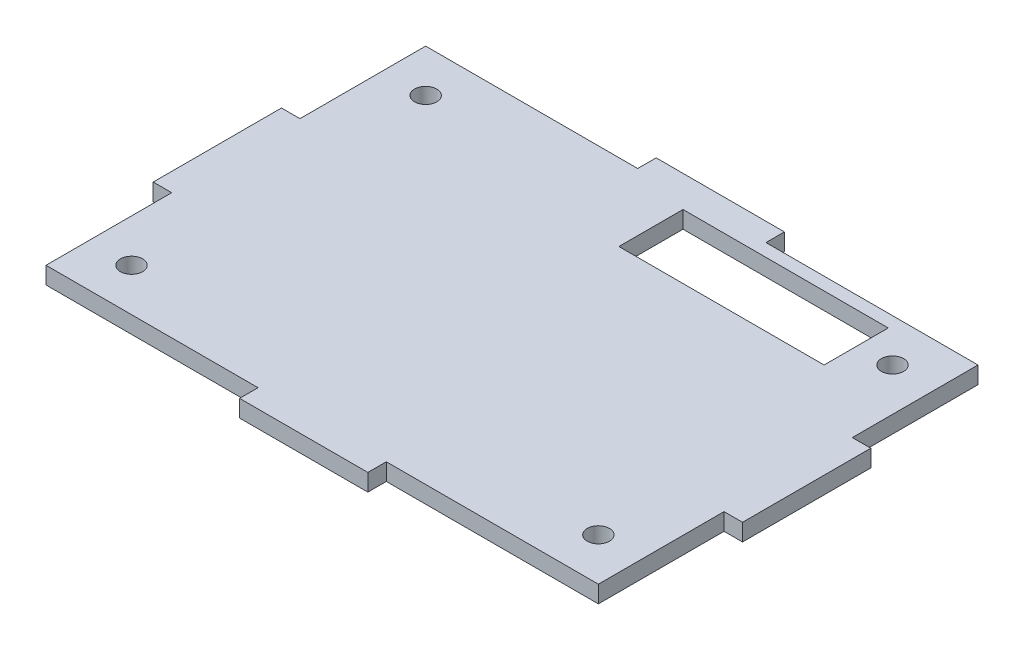
SolidWorks part; units mm, degrees
ref_plane "Front Plane" through (0, 0, 0) normal (0, 0, 1) x (1, 0, 0)
ref_plane "Top Plane" through (0, 0, 0) normal (0, 1, 0) x (1, 0, 0)
ref_plane "Right Plane" through (0, 0, 0) normal (1, 0, 0) x (0, 0, -1)
sketch "Sketch1" plane through (0, 0, 0) normal (0, 1, 0) x (1, 0, 0)
  line L1 (41.021, -28.194) -> (-41.021, -28.194)
  line L2 (41.021, -28.194) -> (41.021, 28.194)
  line L3 (41.021, 28.194) -> (-41.021, 28.194)
  line L4 (-41.021, -28.194) -> (-41.021, 28.194)
  line L5 (41.021, -28.194) -> (-41.021, 28.194) construction
  line L6 (41.021, 28.194) -> (-41.021, -28.194) construction
  line L7 (-34.671, 21.844) -> (34.671, 21.844) construction
  line L8 (-34.671, 21.844) -> (-34.671, -21.844) construction
  line L9 (-34.671, -21.844) -> (34.671, -21.844) construction
  line L10 (34.671, 21.844) -> (34.671, -21.844) construction
  line L11 (-34.671, 21.844) -> (34.671, -21.844) construction
  line L12 (-34.671, -21.844) -> (34.671, 21.844) construction
  circle A0 centre (-34.671, 21.844) radius 1.651
  circle A1 centre (-34.671, -21.844) radius 1.651
  circle A2 centre (34.671, -21.844) radius 1.651
  circle A3 centre (34.671, 21.844) radius 1.651
  point P0 (0, 0)
  point P6 (0, 0)
  dimension "D1" = 3.302
  dimension "D2" = 43.688
  dimension "D3" = 69.342
  dimension "D4" = 6.35
  dimension "D5" = 6.35
  dimension "D6" = 82.042
  dimension "D7" = 56.388
extrude "Boss-Extrude1" add sketch "Sketch1" along normal blind 2.54
sketch "Sketch2" plane through (0, 2.54, 0) normal (0, 1, 0) x (1, 0, 0)
  line L0 (41.021, 28.194) -> (-41.021, 28.194) construction
  line L1 (9.525, 28.194) -> (-9.525, 28.194)
  line L2 (9.525, 28.194) -> (9.525, 30.9372)
  line L3 (9.525, 30.9372) -> (-9.525, 30.9372)
  line L4 (-9.525, 28.194) -> (-9.525, 30.9372)
  line L5 (-41.021, -28.194) -> (41.021, -28.194) construction
  line L6 (-9.525, -28.194) -> (9.525, -28.194)
  line L7 (-9.525, -28.194) -> (-9.525, -30.9372)
  line L8 (-9.525, -30.9372) -> (9.525, -30.9372)
  line L9 (9.525, -28.194) -> (9.525, -30.9372)
  line L10 (41.021, -28.194) -> (41.021, 28.194) construction
  line L11 (41.021, 9.525) -> (43.7642, 9.525)
  line L12 (41.021, 9.525) -> (41.021, -9.525)
  line L13 (41.021, -9.525) -> (43.7642, -9.525)
  line L14 (43.7642, 9.525) -> (43.7642, -9.525)
  line L15 (-41.021, 28.194) -> (-41.021, -28.194) construction
  line L16 (-41.021, 9.525) -> (-43.7642, 9.525)
  line L17 (-41.021, 9.525) -> (-41.021, -9.525)
  line L18 (-41.021, -9.525) -> (-43.7642, -9.525)
  line L19 (-43.7642, 9.525) -> (-43.7642, -9.525)
  line L20 (0, 30.9372) -> (0, -30.9372) construction
  line L21 (-43.7642, 0) -> (43.7642, 0) construction
  dimension "D1" = 2.7432
  dimension "D2" = 19.05
extrude "Boss-Extrude2" add sketch "Sketch2" against normal up to surface (2.54 mm away) up to face at (0, 0, 0)
sketch "Sketch3" plane through (0, 2.54, 0) normal (0, 1, 0) x (1, 0, 0)
  line L0 (34.671, 21.844) -> (29.591, 21.844) construction
  line L1 (-0.889, 26.289) -> (29.591, 26.289)
  line L2 (-0.889, 26.289) -> (-0.889, 16.764)
  line L3 (-0.889, 16.764) -> (29.591, 16.764)
  line L4 (29.591, 26.289) -> (29.591, 16.764)
  line L5 (-0.889, 26.289) -> (29.591, 16.764) construction
  line L6 (-0.889, 16.764) -> (29.591, 26.289) construction
  point P0 (14.351, 21.5265)
  dimension "D1" = 5.08
  dimension "D2" = 5.08
  dimension "D3" = 9.525
  dimension "D4" = 30.48
extrude "Cut-Extrude1" cut sketch "Sketch3" against normal through all
